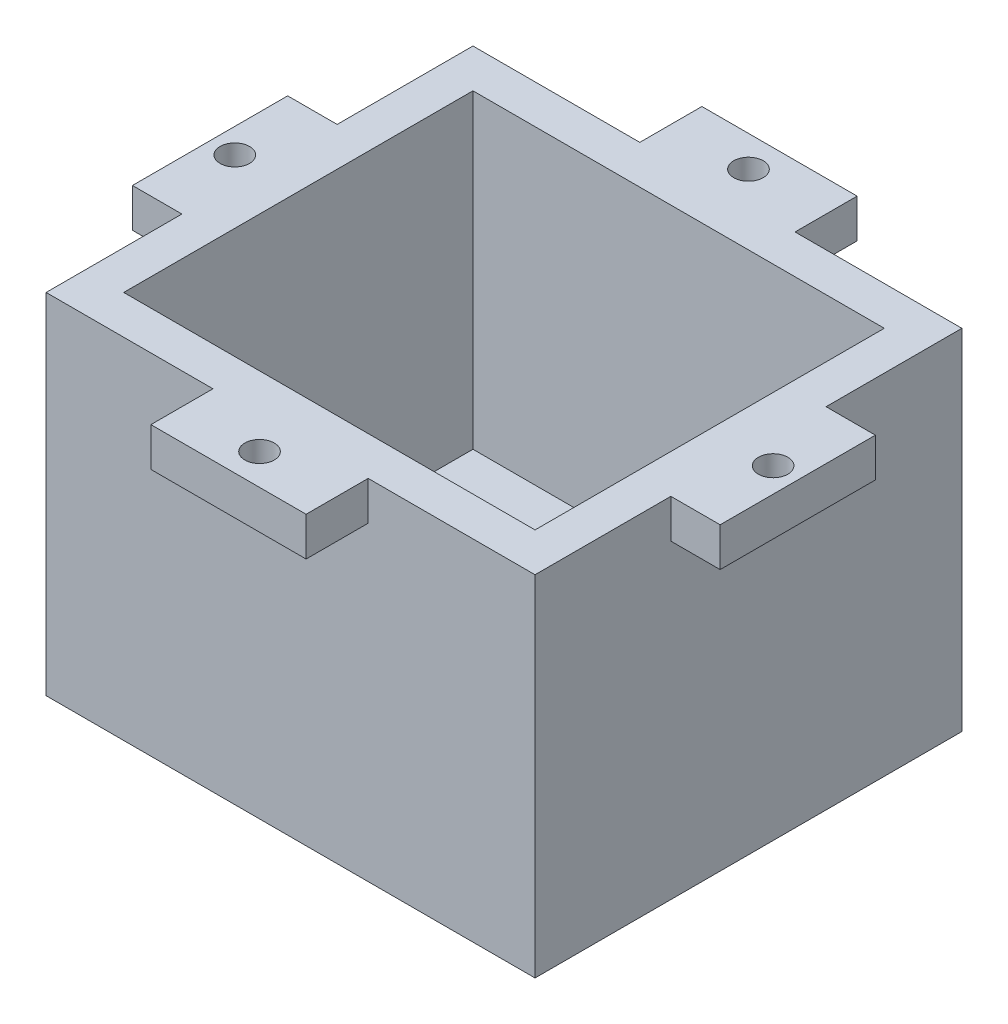
SolidWorks part; units mm, degrees
material "AISI 304"
ref_plane "前视基准面" through (0, 0, 0) normal (0, 0, 1) x (1, 0, 0)
ref_plane "上视基准面" through (0, 0, 0) normal (0, 1, 0) x (1, 0, 0)
ref_plane "右视基准面" through (0, 0, 0) normal (1, 0, 0) x (0, 0, -1)
sketch "Sketch1" plane through (0, 0, 0) normal (0, 1, 0) x (1, 0, 0)
  line L1 (-42.9528, 23.4009) -> (20.0472, 23.4009)
  line L2 (-42.9528, 23.4009) -> (-42.9528, -31.5991)
  line L3 (-42.9528, -31.5991) -> (20.0472, -31.5991)
  line L4 (20.0472, 23.4009) -> (20.0472, -31.5991)
extrude "Boss-Extrude1" add sketch "Sketch1" along normal blind 45
shell "Shell1" thickness 5
sketch "Sketch5" plane through (0, 45, 0) normal (0, 1, 0) x (1, 0, 0)
  line L0 (20.0472, 23.4009) -> (-42.9528, 23.4009) construction
  line L1 (-21.4528, 31.4009) -> (-1.4528, 31.4009)
  line L2 (-21.4528, 31.4009) -> (-21.4528, 23.4009)
  line L3 (-21.4528, 23.4009) -> (-1.4528, 23.4009)
  line L4 (-1.4528, 31.4009) -> (-1.4528, 23.4009)
  line L5 (-42.9528, -31.5991) -> (20.0472, -31.5991) construction
  line L6 (-21.4528, -31.5991) -> (-1.4528, -31.5991)
  line L7 (-21.4528, -31.5991) -> (-21.4528, -39.5991)
  line L8 (-21.4528, -39.5991) -> (-1.4528, -39.5991)
  line L9 (-1.4528, -31.5991) -> (-1.4528, -39.5991)
  line L10 (-42.9528, 23.4009) -> (-42.9528, -31.5991) construction
  line L11 (-42.9528, 5.9009) -> (-49.3282, 5.9009)
  line L12 (-42.9528, 5.9009) -> (-42.9528, -14.0991)
  line L13 (-42.9528, -14.0991) -> (-49.3282, -14.0991)
  line L14 (-49.3282, 5.9009) -> (-49.3282, -14.0991)
  line L15 (20.0472, -31.5991) -> (20.0472, 23.4009) construction
  line L16 (20.0472, 5.9009) -> (26.3972, 5.9009)
  line L17 (20.0472, 5.9009) -> (20.0472, -14.0991)
  line L18 (20.0472, -14.0991) -> (26.3972, -14.0991)
  line L19 (26.3972, 5.9009) -> (26.3972, -14.0991)
  point P6 (-11.4528, 23.4009)
  point P7 (-11.4528, 23.4009)
  point P20 (-42.9528, -4.0991)
  point P21 (-42.9528, -4.0991)
  dimension "D1" = 20
  dimension "D2" = 8
  dimension "D3" = 8
  dimension "D4" = 20
  dimension "D5" = 6.3754
  dimension "D6" = 6.35
extrude "Boss-Extrude3" add sketch "Sketch5" against normal blind 5
hole_wizard "#6 Clearance Hole1" positions "Sketch6" profile "Sketch7" hole size "#6" standard "ANSI Inch" end condition through all
sketch "Sketch6" plane through (0, 40, 0) normal (0, -1, 0) x (-1, 0, 0)
  line L0 (1.4528, -31.5991) -> (21.4528, -31.5991) construction
  line L1 (21.4528, -31.5991) -> (21.4528, -39.5991) construction
  line L2 (1.4528, 23.4009) -> (1.4528, 31.4009) construction
  line L3 (42.9528, 23.4009) -> (42.9528, -31.5991) construction
  line L4 (49.3282, -14.0991) -> (42.9528, -14.0991) construction
  line L5 (-20.0472, -14.0991) -> (-26.3972, -14.0991) construction
  point P0 (11.4528, -35.5991)
  point P5 (11.4528, -31.5991)
  point P9 (21.4528, -35.5991)
  point P10 (11.4528, 27.4009)
  point P15 (1.4528, 27.4009)
  point P16 (46.1405, -4.0991)
  point P21 (42.9528, -4.0991)
  point P25 (46.1405, -14.0991)
  point P26 (-23.2222, -4.0991)
  point P31 (-23.2222, -14.0991)
sketch "Sketch7" plane through (-11.4528, 40, 35.5991) normal (1, 0, 0) x (0, 0, -1)
  line L0 (0, 0) -> (0, 5)
  line L1 (0, 5) -> (1.8986, 5)
  line L2 (1.8986, 5) -> (1.8986, 0)
  line L5 (1.8986, 0) -> (0, 0)
  line L11 (0, -6.35) -> (0, 107.95) construction
  dimension "Thru Hole Dia." = 3.7973
  dimension "Thru Hole Depth" = 5
